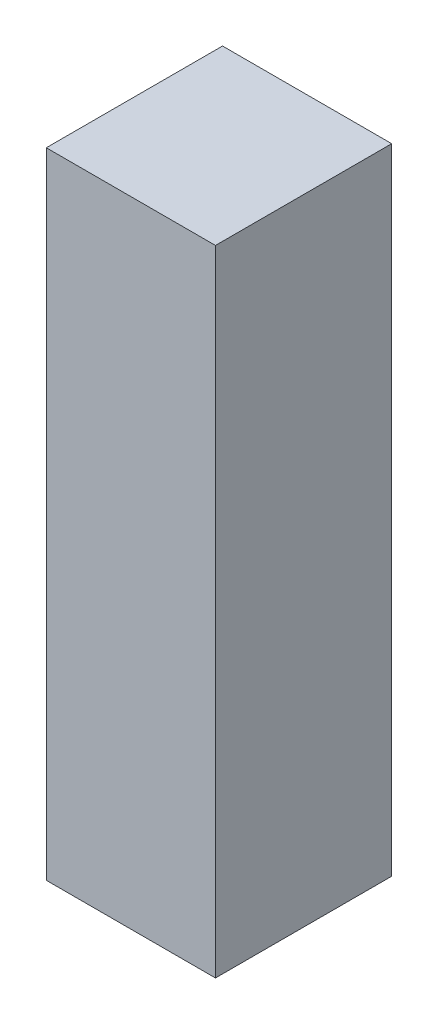
SolidWorks part; units mm, degrees
ref_plane "Front Plane" through (0, 0, 0) normal (0, 0, 1) x (1, 0, 0)
ref_plane "Top Plane" through (0, 0, 0) normal (0, 1, 0) x (1, 0, 0)
ref_plane "Right Plane" through (0, 0, 0) normal (1, 0, 0) x (0, 0, -1)
sketch "Sketch1" plane through (0, 0, 0) normal (0, 1, 0) x (1, 0, 0)
  line L1 (0, 0) -> (12, 0)
  line L2 (0, 0) -> (0, 12.5)
  line L3 (0, 12.5) -> (12, 12.5)
  line L4 (12, 0) -> (12, 12.5)
  dimension "D1" = 12.5
  dimension "D2" = 12
extrude "Boss-Extrude1" add sketch "Sketch1" along normal blind 45
